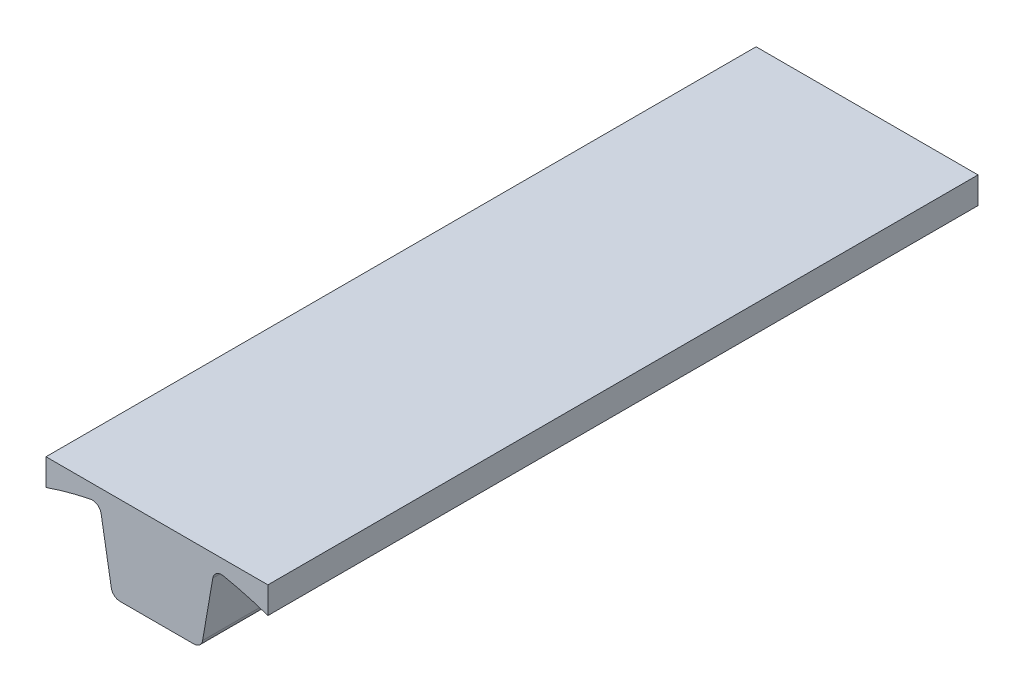
SolidWorks part; units mm, degrees
ref_plane "Front Plane" through (0, 0, 0) normal (0, 0, 1) x (1, 0, 0)
ref_plane "Top Plane" through (0, 0, 0) normal (0, 1, 0) x (1, 0, 0)
ref_plane "Right Plane" through (0, 0, 0) normal (1, 0, 0) x (0, 0, -1)
sketch "Sketch1" plane through (0, 0, 0) normal (0, 0, 1) x (1, 0, 0)
  line L0 (0, 0) -> (0, 114.7095) construction
  line L1 (-12.7, 73.8463) -> (12.7, 73.8463)
  line L2 (12.7, 73.8463) -> (16.4137, 95.4363)
  line L3 (31.75, 91.4846) -> (31.75, 99.1046)
  line L4 (31.75, 99.1046) -> (-31.75, 99.1046)
  line L5 (-31.75, 91.4846) -> (-31.75, 99.1046)
  line L6 (-12.7, 73.8463) -> (-16.4137, 95.4363)
  circle A0 centre (0, 0) radius 96.8375 construction
  arc A1 (16.4137, 95.4363) -> (31.75, 91.4846) centre (0, 0) cw
  arc A2 (-16.4137, 95.4363) -> (-31.75, 91.4846) centre (0, 0) ccw
  point P12 (0, 99.1046)
  point P15 (0, 73.8463)
  dimension "D1" = 193.675
  dimension "D2" = 12.7
  dimension "D3" = 21.59
  dimension "D4" = 99.76
  dimension "D5" = 7.62
  dimension "D6" = 31.75
extrude "Boss-Extrude1" add sketch "Sketch1" along normal blind 203.2
fillet "Fillet1" radius 2.54 1 edges at (16.4137, 95.4363, 101.6)
fillet "Fillet2" radius 2.54 1 edges at (-16.4137, 95.4363, 101.6)
fillet "Fillet3" radius 2.54 2 edges at (-12.7, 73.8463, 101.6) (12.7, 73.8463, 101.6)
sketch "Sketch2" plane through (0, 0, 0) normal (0, 0, -1) x (-1, 0, 0)
  line L0 (-31.75, 91.4846) -> (-31.75, 99.1046) construction
  line L1 (31.75, 99.1046) -> (31.75, 91.4846) construction
  line L2 (-31.75, 99.1046) -> (31.75, 99.1046) construction
  circle A0 centre (-8.89, 92.7546) radius 2.667
  circle A1 centre (8.89, 92.7546) radius 2.667
  circle A2 centre (0, 80.0546) radius 2.667
  dimension "D1" = 5.334
  dimension "D2" = 22.86
  dimension "D3" = 22.86
  dimension "D4" = 6.35
  dimension "D5" = 6.35
  dimension "D6" = 19.05
  dimension "D7" = 31.75
extrude "Cut-Extrude1" cut sketch "Sketch2" against normal blind 11.43 contours A2 | A1 | A0
